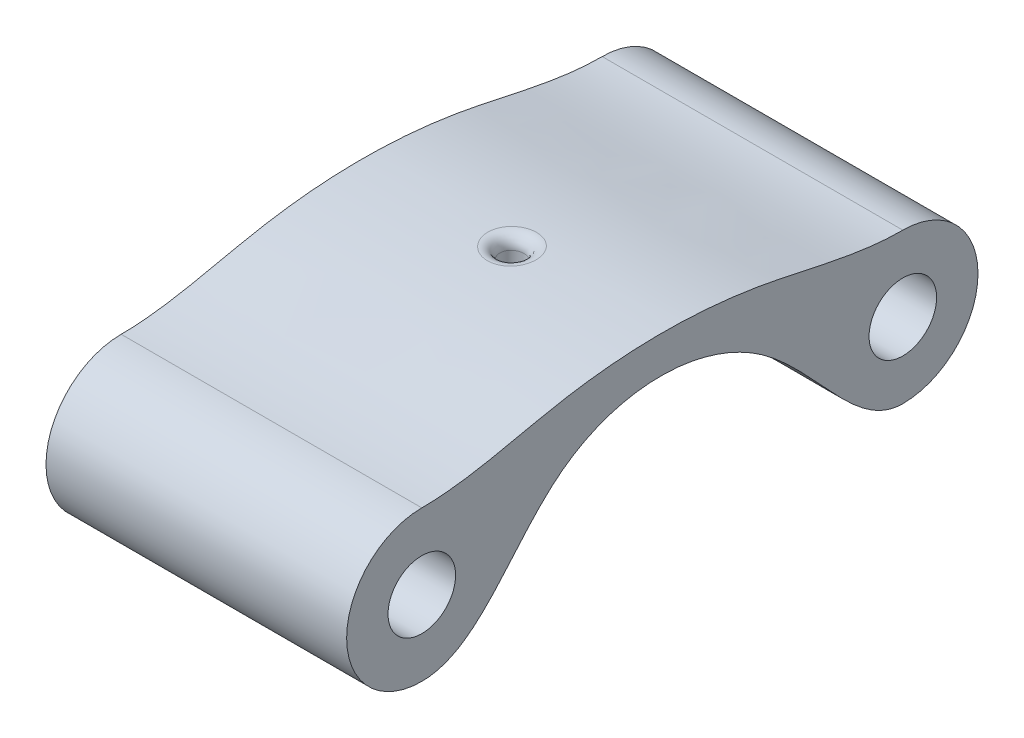
SolidWorks part; units mm, degrees
ref_plane "Front Plane" through (0, 0, 0) normal (0, 0, 1) x (1, 0, 0)
ref_plane "Top Plane" through (0, 0, 0) normal (0, 1, 0) x (1, 0, 0)
ref_plane "Right Plane" through (0, 0, 0) normal (1, 0, 0) x (0, 0, -1)
sketch "Sketch1" plane through (0, 0, 0) normal (1, 0, 0) x (0, 0, -1)
  line L0 (-25.4, 6.35) -> (25.4, 6.35) construction
  line L7 (-10.5237, 2.3918) -> (10.5237, 2.3918) construction
  line L9 (-10.5237, 2.3918) -> (-10.5237, 8.7418) construction
  line L10 (-10.5237, 8.7418) -> (10.5237, 8.7418) construction
  line L11 (10.5237, 2.3918) -> (10.5237, 8.7418) construction
  line L12 (-10.5237, 2.3918) -> (10.5237, 8.7418) construction
  line L13 (-10.5237, 8.7418) -> (10.5237, 2.3918) construction
  arc A0 (-25.4, 6.35) -> (-25.4, -9.525) centre (-25.4, -1.5875) ccw
  arc A1 (25.4, -9.525) -> (25.4, 6.35) centre (25.4, -1.5875) ccw
  arc A2 (-17.4625, -1.5875) -> (-25.4, 6.35) centre (-25.4, -1.5875) ccw construction
  arc A3 (-25.4, -9.525) -> (-17.4625, -1.5875) centre (-25.4, -1.5875) ccw construction
  arc A4 (25.4, 6.35) -> (17.4625, -1.5875) centre (25.4, -1.5875) ccw construction
  arc A5 (17.4625, -1.5875) -> (25.4, -9.525) centre (25.4, -1.5875) ccw construction
  circle A6 centre (-25.4, -1.5875) radius 3.5687
  circle A7 centre (25.4, -1.5875) radius 3.5687
  spline S0 degree 3 poles (-25.4, -9.525) (-19.2856, -9.525) (-12.306, 6.9206) (11.8907, 6.9206) (20.3785, -9.525) (25.4, -9.525) knots 0 0 0 0 0.322142 0.677858 1 1 1 1
  spline S1 degree 3 poles (-25.4, 6.35) (-20.3766, 6.35) (-8.6753, 9.972) (8.6338, 9.972) (20.4572, 6.35) (25.4, 6.35) knots 0 0 0 0 0.294388 0.705612 1 1 1 1
  point P0 (0, 5.5668)
  dimension "D2" = 15.875
  dimension "D5" = 7.1374
  dimension "D1" = 50.8
  dimension "D3" = 6.35
extrude "Boss-Extrude1" add sketch "Sketch1" along normal mid plane 31.75
ref_plane "Plane1" through (0, 0, 0) normal (0, 1, 0) x (1, 0, 0)
sketch "Sketch3" plane through (0, 0, 0) normal (0, 1, 0) x (1, 0, 0)
  circle A0 centre (0, 0) radius 1.27
  dimension "D1" = 2.54
extrude "Cut-Extrude1" cut sketch "Sketch3" against normal through all both and the other way through all
fillet "Fillet1" radius 1.27 1 edges at (0.2918, 9.6515, -1.236)
